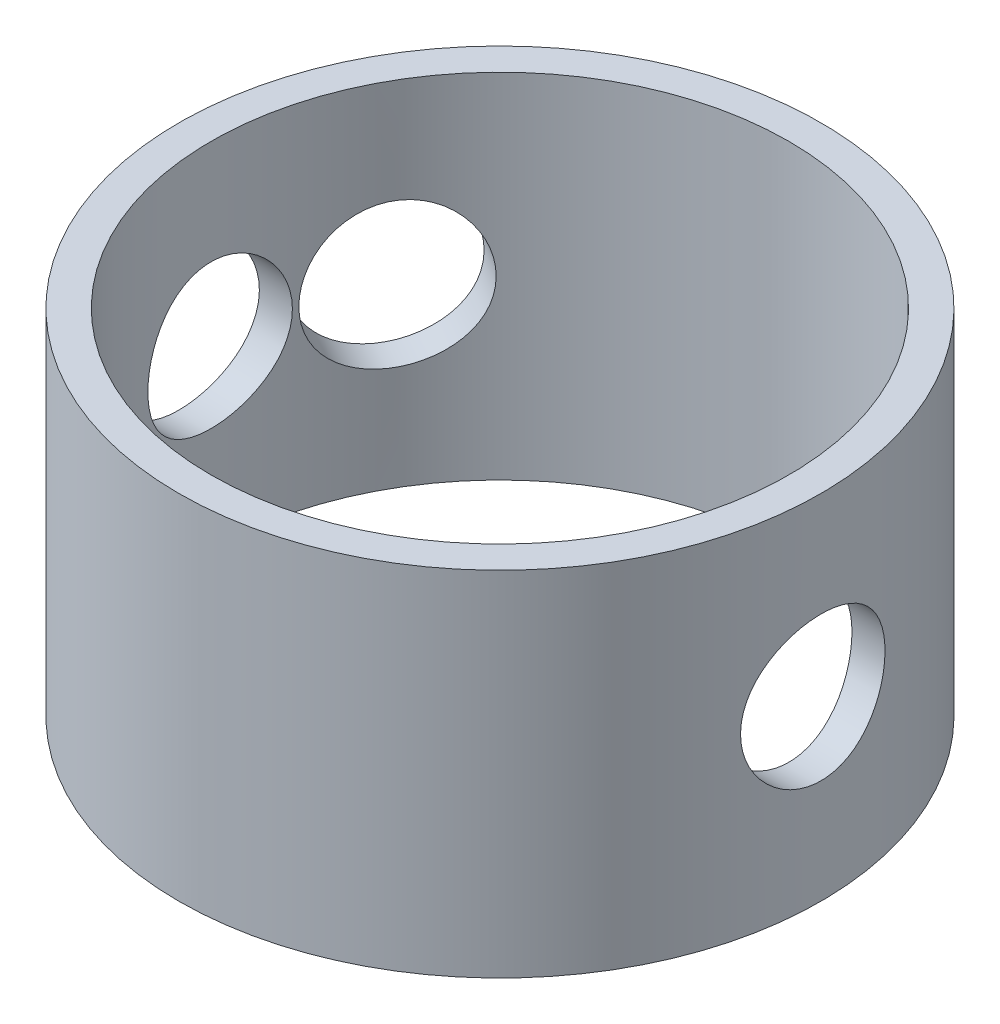
SolidWorks part; units mm, degrees
material "PTFE (geral)"
ref_plane "Plano frontal" through (0, 0, 0) normal (0, 0, 1) x (1, 0, 0)
ref_plane "Plano superior" through (0, 0, 0) normal (0, 1, 0) x (1, 0, 0)
ref_plane "Plano direito" through (0, 0, 0) normal (1, 0, 0) x (0, 0, -1)
sketch "Esboço1" plane through (0, 0, 0) normal (0, 1, 0) x (1, 0, 0)
  line L0 (-22.3434, 0) -> (22.3434, 0) construction
  line L1 (0, 0) -> (-8.6603, 5) construction
  circle A0 centre (0, 0) radius 9
  circle A1 centre (0, 0) radius 10
  point P7 (0, 0)
  dimension "D1" = 18
  dimension "D2" = 20
  dimension "D3" = 30
extrude "Ressalto-extrusão1" add sketch "Esboço1" along normal mid plane 11
ref_plane "Plano1" through (-8.6603, 0, -5) normal (-0.866, 0, -0.5) x (-0.5, 0, 0.866)
sketch "Esboço2" plane through (-8.6603, 0, -5) normal (-0.866, 0, -0.5) x (-0.5, 0, 0.866)
  circle A0 centre (0, 0) radius 2.25
  dimension "D1" = 4.5
extrude "Corte-extrusão1" cut sketch "Esboço2" against normal up to next
sketch "Esboço3" plane through (0, 0, 0) normal (1, 0, 0) x (0, 0, -1)
  circle A0 centre (0, 0) radius 2.25
  dimension "D1" = 4.5
extrude "Corte-extrusão2" cut sketch "Esboço3" against normal through all both and the other way through all contours A0
